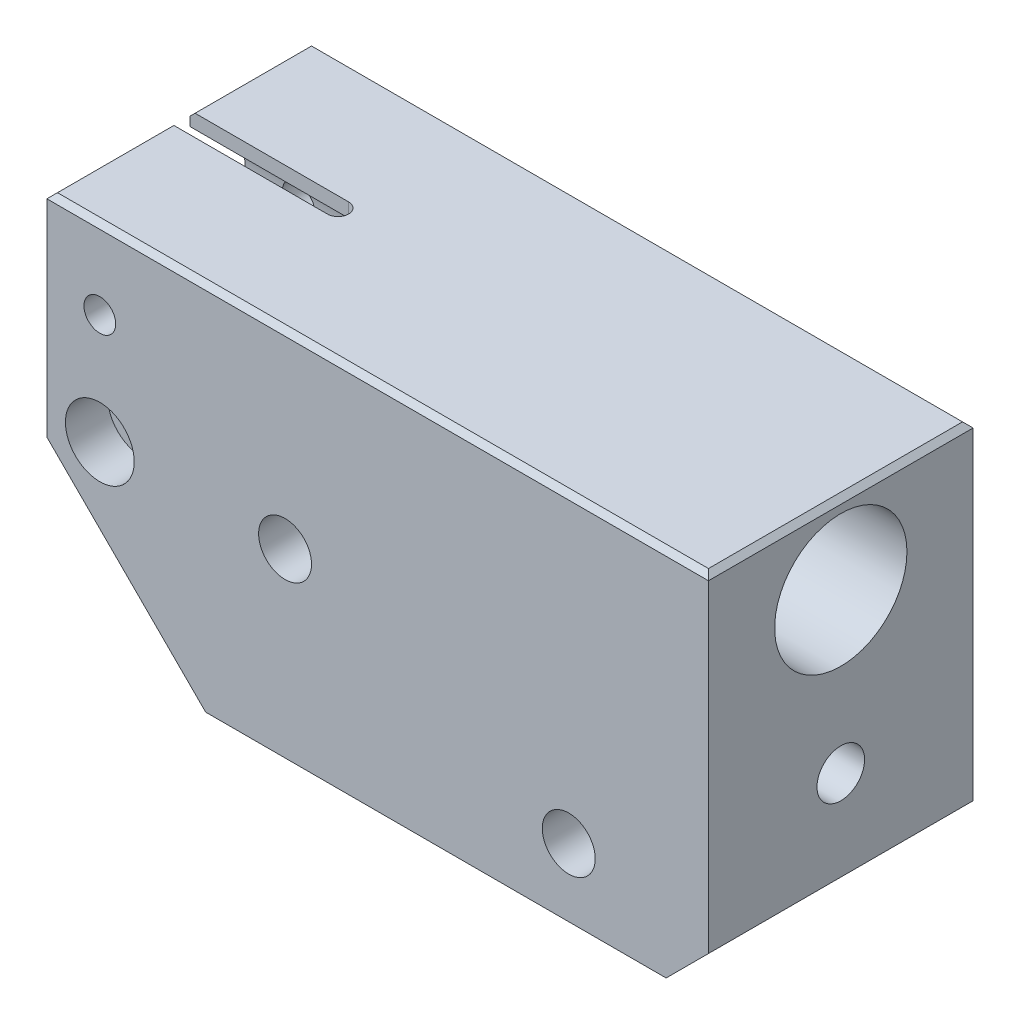
SolidWorks part; units mm, degrees
ref_plane "Alzado" through (0, 0, 0) normal (0, 0, 1) x (1, 0, 0)
ref_plane "Planta" through (0, 0, 0) normal (0, 1, 0) x (1, 0, 0)
ref_plane "Vista lateral" through (0, 0, 0) normal (1, 0, 0) x (0, 0, -1)
sketch "Croquis1" plane through (0, 0, 0) normal (0, 0, 1) x (1, 0, 0)
  line L0 (0, 0) -> (125, 0)
  line L1 (125, 0) -> (125, -62)
  line L2 (125, -62) -> (117, -70)
  line L3 (117, -70) -> (30, -70)
  line L4 (30, -70) -> (0, -40)
  line L5 (0, -40) -> (0, 0)
  circle A0 centre (10, -15) radius 3
  circle A1 centre (10, -35.8) radius 4
  circle A2 centre (45, -35.8) radius 5
  circle A3 centre (98.6, -57.2) radius 5
  dimension "D8" = 6
  dimension "D13" = 8
  dimension "D15" = 10
  dimension "D16" = 10
  dimension "D1" = 125
  dimension "D2" = 70
  dimension "D3" = 8
  dimension "D4" = 90
  dimension "D5" = 8
  dimension "D6" = 30
  dimension "D7" = 30
  dimension "D9" = 15
  dimension "D10" = 10
  dimension "D11" = 10
  dimension "D12" = 35.8
  dimension "D14" = 35
  dimension "D17" = 26.4
  dimension "D18" = 57.2
extrude "Saliente-Extruir1" add sketch "Croquis1" along normal mid plane 50
chamfer "Chaflán1" distance 1 angle 45 4 edges at (125, 0, 0) (62.5, 0, -25) (0, 0, 0) (62.5, 0, 25)
sketch "Croquis2" plane through (0, 0, 0) normal (0, 1, 0) x (1, 0, 0)
  line L0 (31.1963, 0) -> (0, 0) construction
  line L1 (30, 2) -> (-5.3163, 2)
  line L2 (-5.3163, 2) -> (-5.3163, -2)
  line L3 (-5.3163, -2) -> (30, -2)
  line L4 (0, -25) -> (0, 25) construction
  arc A0 (30, -2) -> (30, 2) centre (30, 0) ccw
  dimension "D1" = 4
  dimension "D2" = 30
  dimension "D3" = 2
  dimension "D4" = 5.3163
extrude "Cortar-Extruir1" cut sketch "Croquis2" against normal blind 94.3
sketch "Croquis3" plane through (0, 0, 2) normal (0, 0, -1) x (-1, 0, 0)
  circle A0 centre (-10, -35.8) radius 4.25
  dimension "D1" = 8.5
extrude "Cortar-Extruir2" cut sketch "Croquis3" against normal blind 94.3
sketch "Croquis4" plane through (0, 0, 25) normal (0, 0, 1) x (1, 0, 0)
  circle A0 centre (10, -35.8) radius 6.5
  dimension "D1" = 13
extrude "Cortar-Extruir3" cut sketch "Croquis4" against normal blind 8
sketch "Croquis5" plane through (125, 0, 0) normal (1, 0, 0) x (0, 0, -1)
  line L0 (-25, -62) -> (-25, -1) construction
  line L1 (-24, 0) -> (24, 0) construction
  circle A0 centre (0, -15) radius 12.5
  dimension "D1" = 25
  dimension "D2" = 25
  dimension "D3" = 15
extrude "Cortar-Extruir4" cut sketch "Croquis5" against normal blind 141.5
hole_wizard "Taladro roscado M10x1.01" positions "Croquis7" profile "Croquis6" tap size "M10x1.0" standard "DIN"
sketch "Croquis7" plane through (125, 0, 0) normal (1, 0, 0) x (0, 0, -1)
  line L0 (-25, -62) -> (-25, -1) construction
  line L1 (-24, 0) -> (24, 0) construction
  point P0 (0, -45)
  dimension "D1" = 25
  dimension "D2" = 45
sketch "Croquis6" plane through (125, -45, 0) normal (0, 1, 0) x (0, 0, -1)
  line L0 (0, 0) -> (0, 22.7039)
  line L1 (0, 22.7039) -> (4.5, 20)
  line L2 (4.5, 20) -> (4.5, 0)
  line L5 (4.5, 0) -> (0, 0)
  line L10 (0, 22.7039) -> (-4.5, 20) construction
  line L11 (0, -6.35) -> (0, 107.95) construction
  dimension "Diámetro de perforador para roscar" = 9
  dimension "Profundidad de perforador para roscar" = 20
  dimension "Ángulo de perforador" = 118
cosmetic thread "Rosca de taladro1" parameters "D1"=20, "D2"=10
